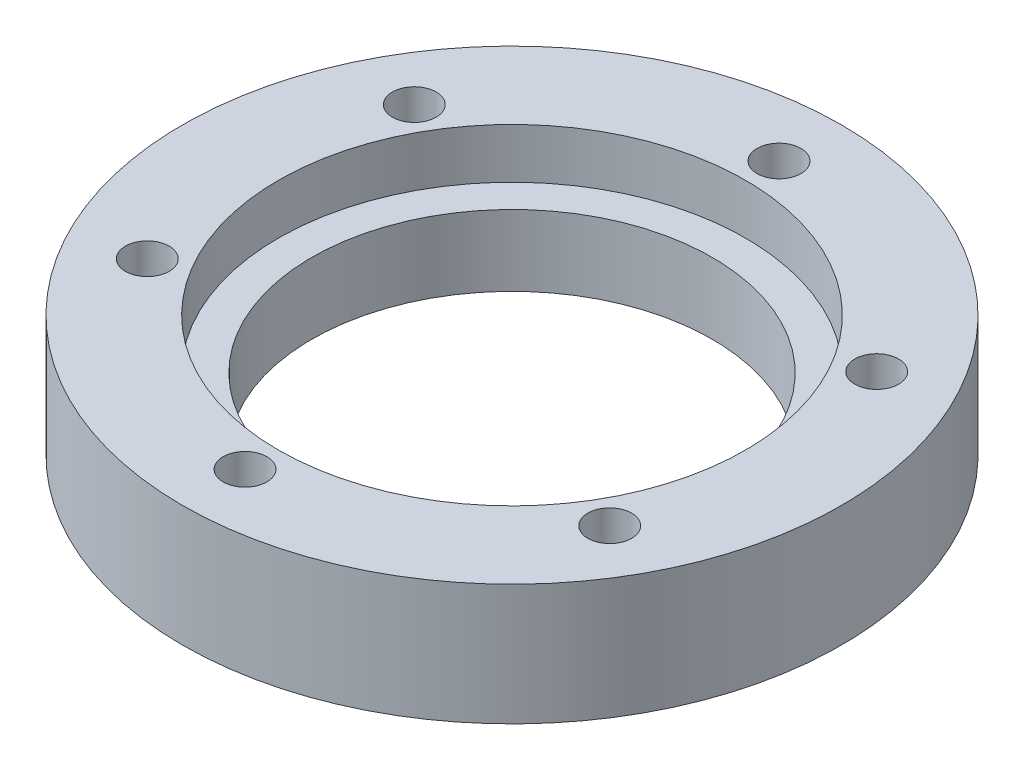
SolidWorks part; units mm, degrees
ref_plane "Front Plane" through (0, 0, 0) normal (0, 0, 1) x (1, 0, 0)
ref_plane "Top Plane" through (0, 0, 0) normal (0, 1, 0) x (1, 0, 0)
ref_plane "Right Plane" through (0, 0, 0) normal (1, 0, 0) x (0, 0, -1)
sketch "Sketch1" plane through (0, 0, 0) normal (0, 1, 0) x (1, 0, 0)
  circle A0 centre (0, 0) radius 79
extrude "Boss-Extrude1" add sketch "Sketch1" along normal blind 29
hole_wizard "CBORE for M5 Hex Head Bolt1" positions "Sketch2" profile "Sketch3" counterbore size "M5" standard "ANSI Metric" end condition through all
sketch "Sketch2" plane through (0, 29, 0) normal (0, 1, 0) x (1, 0, 0)
  point P0 (0, 0)
sketch "Sketch3" plane through (0, 29, 0) normal (1, 0, 0) x (0, 0, 1)
  line L0 (0, 0) -> (0, 29)
  line L1 (0, 29) -> (48, 29)
  line L3 (48, 29) -> (48, 12)
  line L4 (48, 12) -> (56, 12)
  line L5 (56, 12) -> (56, 0)
  line L7 (56, 0) -> (0, 0)
  line L11 (0, -6.35) -> (0, 107.95) construction
  dimension "Thru Hole Dia." = 96
  dimension "Thru Hole Depth" = 29
  dimension "C'Bore Dia." = 112
  dimension "C'Bore Depth" = 12
hole_wizard "M12x1.5 Tapped Hole1" positions "Sketch4" profile "Sketch5" tap size "M12x1.5" standard "ANSI Metric" end condition through all
sketch "Sketch4" plane through (0, 29, 0) normal (0, 1, 0) x (1, 0, 0)
  line L0 (0, 0) -> (55.4256, -32) construction
  circle A0 centre (0, 0) radius 64 construction
  point P0 (55.4256, -32)
  point P14 (0, 0)
sketch "Sketch5" plane through (55.4256, 29, 32) normal (1, 0, 0) x (0, 0, 1)
  line L0 (0, 0) -> (0, 29)
  line L1 (0, 29) -> (5.25, 29)
  line L2 (5.25, 29) -> (5.25, 0)
  line L5 (5.25, 0) -> (0, 0)
  line L11 (0, -6.35) -> (0, 107.95) construction
  dimension "Thru Tap Drill Dia." = 10.5
  dimension "Thru Tap Drill Depth" = 29
cosmetic thread "Hole Thread1" parameters "D2"=12
sketch "Sketch6" plane through (0, 29, 0) normal (0, 1, 0) x (1, 0, 0)
  circle A0 centre (0, 0) radius 64 construction
pattern_circular "CirPattern2" count 6 over 360 about axis through (0, 0, 0) along (0, 1, 0) of "M12x1.5 Tapped Hole1"
